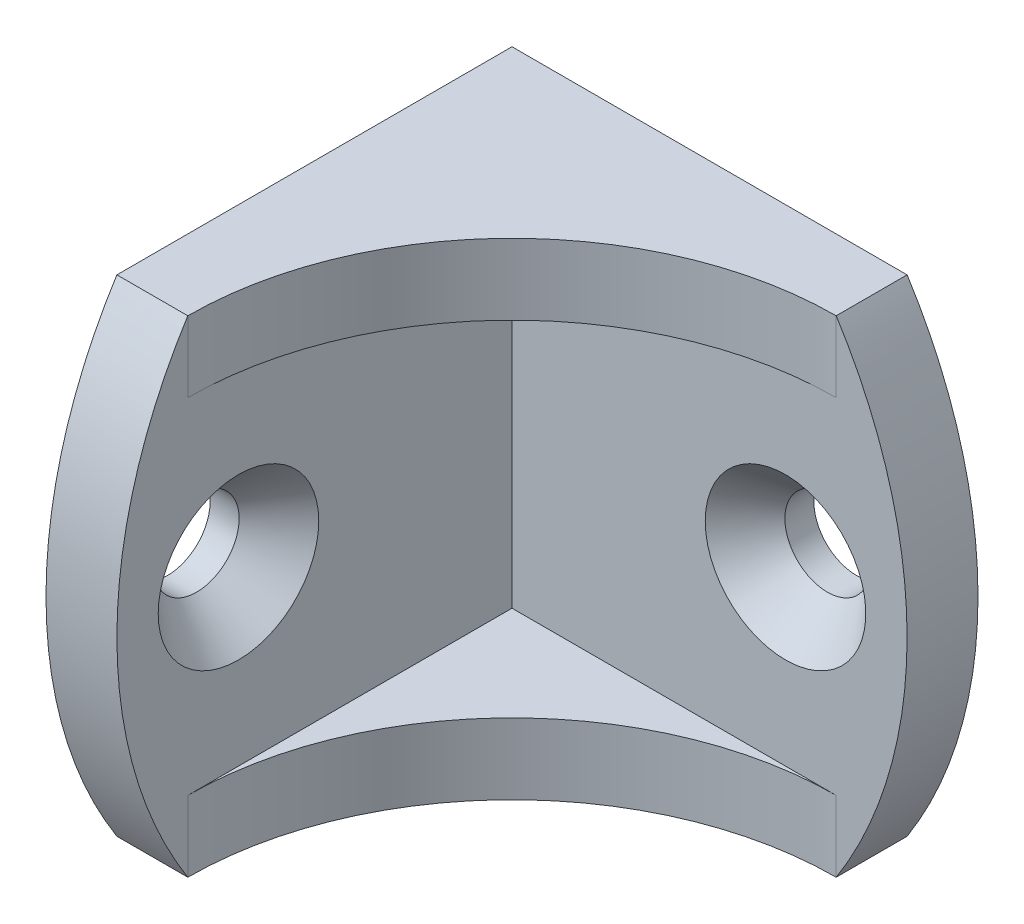
SolidWorks part; units mm, degrees
ref_plane "Front Plane" through (0, 0, 0) normal (0, 0, 1) x (1, 0, 0)
ref_plane "Top Plane" through (0, 0, 0) normal (0, 1, 0) x (1, 0, 0)
ref_plane "Right Plane" through (0, 0, 0) normal (1, 0, 0) x (0, 0, -1)
sketch "Sketch1" plane through (0, 0, 0) normal (0, 1, 0) x (1, 0, 0)
  line L0 (0, 0) -> (0, -23)
  line L1 (0, 0) -> (23, 0)
  line L2 (0, -23) -> (3.5, -23) construction
  line L3 (3.5, -23) -> (3.5, -19.5) construction
  line L4 (23, 0) -> (23, -3.5) construction
  line L5 (23, -3.5) -> (19.5, -3.5) construction
  line L6 (0, 0) -> (23, -23) construction
  circle A0 centre (0, -17) radius 2.1
  circle A1 centre (17, 0) radius 2.1
  arc A2 (19.5, -3.5) -> (3.5, -19.5) centre (19.5, -19.5) ccw construction
  circle A3 centre (0, -17) radius 3.9624 construction
  point P3 (0, -17)
  point P6 (17, 0)
  point P11 (14.9, 0)
  point P12 (19.1, 0)
  point P13 (0, -14.9)
  point P14 (0, -19.1)
  point P20 (0, -20.9624)
  point P21 (0, -13.0376)
  dimension "Hole Size" = 4.2
  dimension "CS" = 7.9248
  dimension "Length (A)" = 23
  dimension "Length (B)" = 23
  dimension "Thickness" = 3.5
  dimension "D4" = 17
  dimension "Hole Location" = 17
  dimension "D1" = 3.5
sketch "Sketch2" plane through (0, 0, 0) normal (0, 0, 1) x (1, 0, 0)
  line L0 (23, 12) -> (23, -12)
  point P3 (23, 0)
  dimension "Length (C)" = 24
ref_axis "Axis1" through (0, 0, 0) along (0.7071, 0, 0.7071)
sketch "Sketch3" plane through (0, 0, 0) normal (0, 1, 0) x (1, 0, 0)
  line L0 (0, -23) -> (3.5, -23) construction
  line L1 (3.5, -23) -> (3.5, -19.5) construction
  line L2 (23, -3.5) -> (19.5, -3.5) construction
  line L3 (23, 0) -> (23, -3.5) construction
  line L4 (0, 0) -> (23, 0) construction
  line L5 (0, 0) -> (0, -23) construction
  line L6 (0, -23) -> (3.5, -23)
  line L7 (3.5, -23) -> (3.5, -3.5)
  line L8 (23, -3.5) -> (3.5, -3.5)
  line L9 (23, 0) -> (23, -3.5)
  line L10 (0, 0) -> (23, 0)
  line L11 (0, 0) -> (0, -23)
extrude "Boss-Extrude1" add sketch "Sketch3" along normal up to vertex (12 mm away) and the other way up to vertex (12 mm away) up to point (23, 12, 0) other way up to point (23, -12, 0)
sketch "Sketch8" plane through (0, 12, 0) normal (0, 1, 0) x (1, 0, 0)
  line L0 (3.5, -3.5) -> (23, -3.5) construction
  line L1 (3.5, -23) -> (3.5, -3.5) construction
  line L2 (3.5, -3.5) -> (19.5, -3.5)
  line L3 (3.5, -19.5) -> (3.5, -3.5)
  arc A0 (19.5, -3.5) -> (3.5, -19.5) centre (19.5, -19.5) ccw construction
  arc A1 (19.5, -3.5) -> (3.5, -19.5) centre (19.5, -19.5) ccw
extrude "Boss-Extrude2" add sketch "Sketch8" against normal blind 3.5
mirror "Mirror1" about plane through (0, 0, 0) normal (0, 1, 0) of "Boss-Extrude2"
sketch "Sketch7" plane through (3.5, 0, 0) normal (1, 0, 0) x (0, 0, -1)
  line L0 (-23, 12) -> (-23, -12) construction
  line L1 (-19.5, 8.5) -> (-19.5, 12) construction
  arc A0 (-19.5, 12) -> (-19.5, -12) centre (-0.6786, 0) ccw
extrude "Cut-Extrude3" cut sketch "Sketch7" against normal through all both and the other way through all flip side to cut
sketch "Sketch5" plane through (3.5, 0, 0) normal (1, 0, 0) x (0, 0, -1)
  circle A0 centre (-17, 0) radius 2.1
extrude "Cut-Extrude1" cut sketch "Sketch5" against normal through all both and the other way through all
sketch "Sketch6" plane through (3.5, 0, 0) normal (1, 0, 0) x (0, 0, -1)
  circle A0 centre (-17, 0) radius 3.9624
extrude "Cut-Extrude2" cut sketch "Sketch6" against normal up to vertex (3.5 mm away) draft 42 and the other way blind 3.048 draft 42 up to point (0, 0, 20.9624)
pattern_circular "CirPattern2" count 2 over 180 about axis through (0, 0, 0) along (0.7071, 0, 0.7071) of "Cut-Extrude2", "Cut-Extrude1", "Cut-Extrude3"
equation "\"D4@Sketch1\"=\"Hole Location@Sketch1\""
equation "\"D1@Sketch1\"=\"Thickness@sketch1\""
equation "\"D1@Boss-Extrude2\"=\"Thickness@sketch1\""
